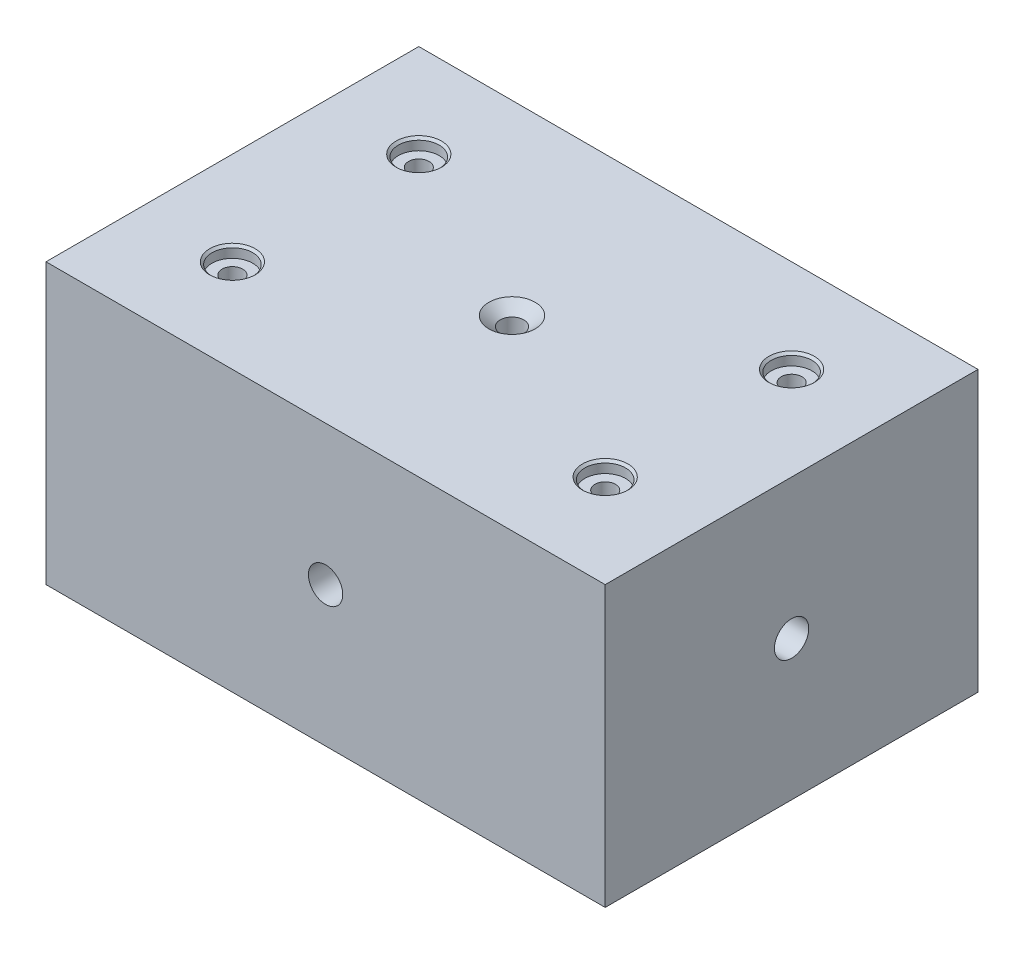
SolidWorks part; units mm, degrees
ref_plane "Front Plane" through (0, 0, 0) normal (0, 0, 1) x (1, 0, 0)
ref_plane "Top Plane" through (0, 0, 0) normal (0, 1, 0) x (1, 0, 0)
ref_plane "Right Plane" through (0, 0, 0) normal (1, 0, 0) x (0, 0, -1)
sketch "Sketch1" plane through (0, 0, 0) normal (0, 1, 0) x (1, 0, 0)
  line L1 (-76.2, -50.8) -> (76.2, -50.8)
  line L2 (-76.2, -50.8) -> (-76.2, 50.8)
  line L3 (-76.2, 50.8) -> (76.2, 50.8)
  line L4 (76.2, -50.8) -> (76.2, 50.8)
  line L5 (-76.2, -50.8) -> (76.2, 50.8) construction
  line L6 (-76.2, 50.8) -> (76.2, -50.8) construction
  point P0 (0, 0)
  dimension "D1" = 101.6
  dimension "D2" = 152.4
extrude "Boss-Extrude1" add sketch "Sketch1" along normal blind 76.2
hole_wizard "CBORE for #10 Binding Head Machine Screw2" positions "Sketch6" profile "Sketch7" counterbore size "#10" standard "ANSI Inch" end condition through all
sketch "Sketch6" plane through (0, 76.2, 0) normal (0, 1, 0) x (1, 0, 0)
  line L0 (76.2, 50.8) -> (-76.2, 50.8) construction
  line L1 (-76.2, 50.8) -> (-76.2, -50.8) construction
  line L2 (-76.2, 0) -> (76.2, 0) construction
  line L3 (76.2, -50.8) -> (76.2, 50.8) construction
  line L5 (0, 50.8) -> (0, -50.8) construction
  line L6 (-76.2, -50.8) -> (76.2, -50.8) construction
  point P0 (-50.8, 25.4)
  point P19 (50.8, 25.4)
  point P20 (50.8, -25.4)
  point P21 (-50.8, -25.4)
  dimension "D1" = 25.4
  dimension "D2" = 25.4
sketch "Sketch7" plane through (-50.8, 76.2, -25.4) normal (1, 0, 0) x (0, 0, 1)
  line L0 (0, 0) -> (0, 76.2)
  line L1 (0, 76.2) -> (2.8067, 76.2)
  line L3 (2.8067, 76.2) -> (2.8067, 3.1242)
  line L4 (5.5562, 3.1242) -> (2.8067, 3.1242)
  line L5 (5.5562, 3.1242) -> (5.5562, 0.635)
  line L6 (5.5562, 0.635) -> (6.1912, 0)
  line L7 (6.1912, 0) -> (0, 0)
  line L8 (-5.5562, 0.635) -> (-6.1912, 0) construction
  line L11 (0, -6.35) -> (0, 107.95) construction
  dimension "Thru Hole Dia." = 5.6134
  dimension "Thru Hole Depth" = 76.2
  dimension "C'Bore Dia." = 11.1125
  dimension "C'Bore Depth" = 3.1242
  dimension "Near C'Sink Dia." = 12.3825
  dimension "Near C'Sink Angle" = 90
hole_wizard "CSK for M6 Flat Head Machine Screw1" positions "Sketch8" profile "Sketch9" countersink size "M6" standard "ANSI Metric"
sketch "Sketch8" plane through (0, 76.2, 0) normal (0, 1, 0) x (1, 0, 0)
  point P0 (0, 0)
sketch "Sketch9" plane through (0, 76.2, 0) normal (1, 0, 0) x (0, 0, 1)
  line L0 (0, 0) -> (0, 52.7228)
  line L1 (0, 52.7228) -> (3.2, 50.8)
  line L2 (3.2, 50.8) -> (3.2, 2.6012)
  line L3 (3.2, 2.6012) -> (6.3, 0)
  line L5 (6.3, 0) -> (0, 0)
  line L6 (-3.2, 2.6012) -> (-6.3, 0) construction
  line L10 (0, 52.7228) -> (-3.2, 50.8) construction
  line L11 (0, -6.35) -> (0, 107.95) construction
  dimension "Hole Dia." = 6.4
  dimension "Hole Depth" = 50.8
  dimension "Near C'Sink Dia." = 12.6
  dimension "Near C'Sink Angle" = 100
  dimension "Drill Angle" = 118
hole_wizard "7/16-14 Tapped Hole1" positions "3DSketch1" profile "Sketch10" tap size "7/16-14" standard "ANSI Inch" end condition through all
sketch3d "3DSketch1"
  line L0 (-76.2, 38.1, 50.8) -> (76.2, 38.1, 50.8) construction
  line L1 (-76.2, 76.2, 50.8) -> (-76.2, 0, 50.8) construction
  line L2 (76.2, 76.2, 50.8) -> (76.2, 0, 50.8) construction
  line L4 (0, 76.2, 50.8) -> (0, 0, 50.8) construction
  line L5 (-76.2, 76.2, 50.8) -> (76.2, 76.2, 50.8) construction
  line L6 (-76.2, 0, 50.8) -> (76.2, 0, 50.8) construction
  line L9 (76.2, 76.2, 0) -> (0, 0, 0) construction
  line L10 (76.2, 76.2, 50.8) -> (76.2, 76.2, -50.8) construction
  line L12 (76.2, 38.1, -50.8) -> (76.2, 38.1, 50.8) construction
  line L13 (76.2, 76.2, -50.8) -> (76.2, 0, -50.8) construction
  point P0 (0, 38.1, 50.8)
  point P2 (76.2, 38.1, 0)
  point P34 (76.2, 38.1, 0)
sketch "Sketch10" plane through (0, 38.1, 50.8) normal (1, 0, 0) x (0, -1, 0)
  line L0 (0, 0) -> (0, 101.6)
  line L1 (0, 101.6) -> (4.6736, 101.6)
  line L2 (4.6736, 101.6) -> (4.6736, 0)
  line L5 (4.6736, 0) -> (0, 0)
  line L11 (0, -6.35) -> (0, 107.95) construction
  dimension "Thru Tap Drill Dia." = 9.3472
  dimension "Thru Tap Drill Depth" = 101.6
cosmetic thread "Hole Thread1" parameters "D1"=76.2, "D2"=11.1125
cosmetic thread "Hole Thread2" parameters "D1"=76.2, "D2"=11.1125
